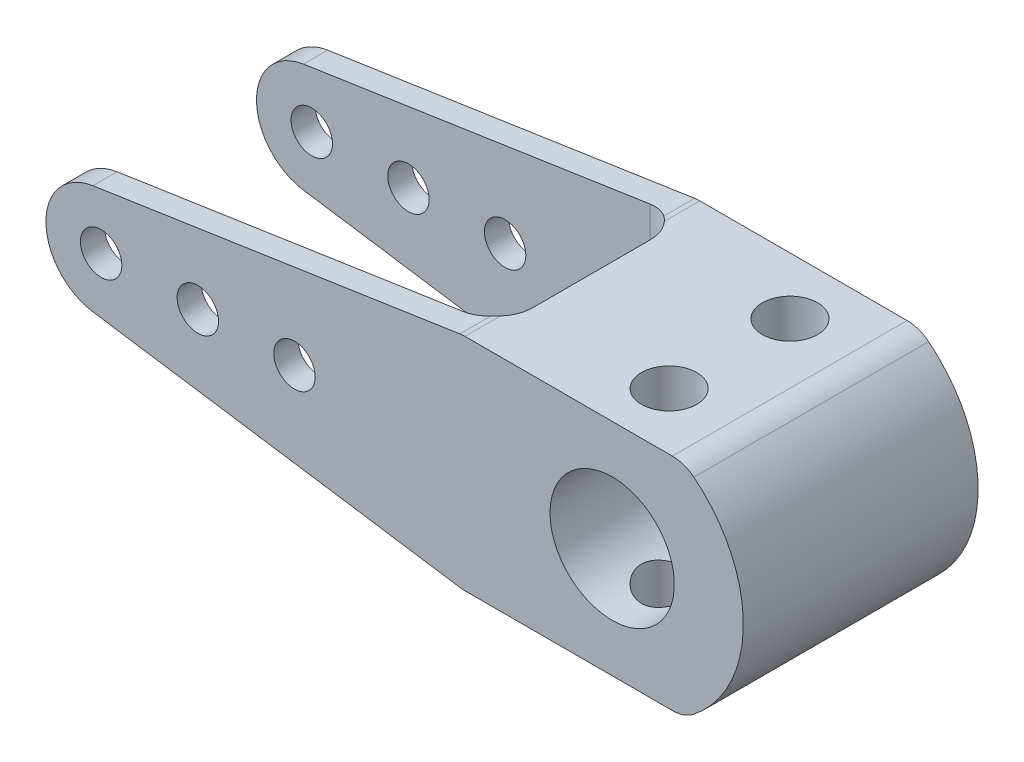
SolidWorks part; units mm, degrees
material "6061-T6 (SS)"
ref_plane "前基準面" through (0, 0, 0) normal (0, 0, 1) x (1, 0, 0)
ref_plane "上基準面" through (0, 0, 0) normal (0, 1, 0) x (1, 0, 0)
ref_plane "右基準面" through (0, 0, 0) normal (1, 0, 0) x (0, 0, -1)
sketch "草圖1" plane through (0, 0, 0) normal (0, 0, 1) x (1, 0, 0)
  line L0 (-2.8243, 18.7889) -> (-75.1892, 7.9111)
  line L1 (-2.8243, -18.7889) -> (-75.1892, -7.9111)
  line L2 (-21.682, 15.9543) -> (10.318, 15.9543)
  line L3 (-21.682, -15.9543) -> (10.318, -15.9543)
  line L4 (10.318, 15.9543) -> (10.318, -15.9543)
  line L5 (-21.682, 15.9543) -> (-21.682, -15.9543)
  circle A1 centre (0, 0) radius 19 construction
  arc A2 (-2.8243, 18.7889) -> (-2.8243, -18.7889) centre (0, 0) cw
  circle A3 centre (-74, 0) radius 8 construction
  arc A4 (-75.1892, -7.9111) -> (-75.1892, 7.9111) centre (-74, 0) cw
  circle A5 centre (-74, 0) radius 3
  circle A9 centre (-60, 0) radius 3
  circle A10 centre (-46, 0) radius 3
  dimension "D1" = 60
  dimension "D2" = 19
  dimension "D3" = 6
  dimension "D4" = 14
  dimension "D6" = 8
  dimension "D7" = 32
  dimension "D5" = 3
extrude "填料-伸長1" add sketch "草圖1" along normal blind 34 contours A4 L1 L5 L0 A10 A9 A5 | L2 L5 L3 L4 | A2 L4
sketch "草圖3" plane through (0, 0, 0) normal (0, 0, -1) x (-1, 0, 0)
  circle A0 centre (0, 0) radius 9
  dimension "D1" = 18
sketch "草圖4" plane through (0, 0, 0) normal (0, 0, -1) x (-1, 0, 0)
  line L1 (20, -25) -> (90, -25)
  line L2 (20, -25) -> (20, 25)
  line L3 (20, 25) -> (90, 25)
  line L4 (90, -25) -> (90, 25)
  dimension "D1" = 50
  dimension "D2" = 20
  dimension "D3" = 70
  dimension "D4" = 25
extrude "除料-伸長3" cut sketch "草圖4" against normal blind 27 from offset 3.5 offset against normal yes
fillet "圓角1" radius 5 2 edges at (-20, 0, 3.5) (-20, 0, 30.5)
ref_plane "平面1" through (0, 0, 17) normal (0, 0, 1) x (1, 0, 0)
extrude "除料-伸長5" cut sketch "草圖3" against normal through all
sketch "草圖7" plane through (0, 0, 17) normal (0, 0, 1) x (1, 0, 0)
  line L0 (-60, 0) -> (-60, 34.6821)
sketch "草圖8" plane through (0, 0, 0) normal (0, 1, 0) x (1, 0, 0)
  line L0 (0, 0) -> (0, -8.25) construction
  line L1 (0, -8.25) -> (0, -25.75) construction
  line L2 (0, -25.75) -> (0, -34) construction
  line L4 (-21.682, -34) -> (10.318, -34) construction
  circle A0 centre (0, -25.75) radius 4
  circle A1 centre (0, -8.25) radius 4
  dimension "D1" = 17.5
  dimension "D3" = 8
extrude "除料-伸長6" cut sketch "草圖8" against normal mid plane 40 contours A0 | A1
sketch "草圖9" plane through (0, 0, 0) normal (0, 1, 0) x (1, 0, 0)
  line L0 (0, -25.75) -> (0, -8.25) construction
  line L2 (-8.5, -34) -> (8.5, -34)
  line L3 (-8.5, -34) -> (-8.5, 0)
  line L4 (-8.5, 0) -> (8.5, 0)
  line L5 (8.5, -34) -> (8.5, 0)
  line L6 (-8.5, -34) -> (8.5, 0) construction
  line L7 (-8.5, 0) -> (8.5, -34) construction
  point P4 (0, -17)
  dimension "D1" = 17
  dimension "D2" = 34
fillet "圓角2" radius 5 6 edges at (-21.682, -15.9543, 2.3798) (-21.682, -15.9543, 31.6202) (-21.682, 15.9543, 2.3798) (-21.682, 15.9543, 31.6202) (10.318, -15.9543, 17) (10.318, 15.9543, 17)
